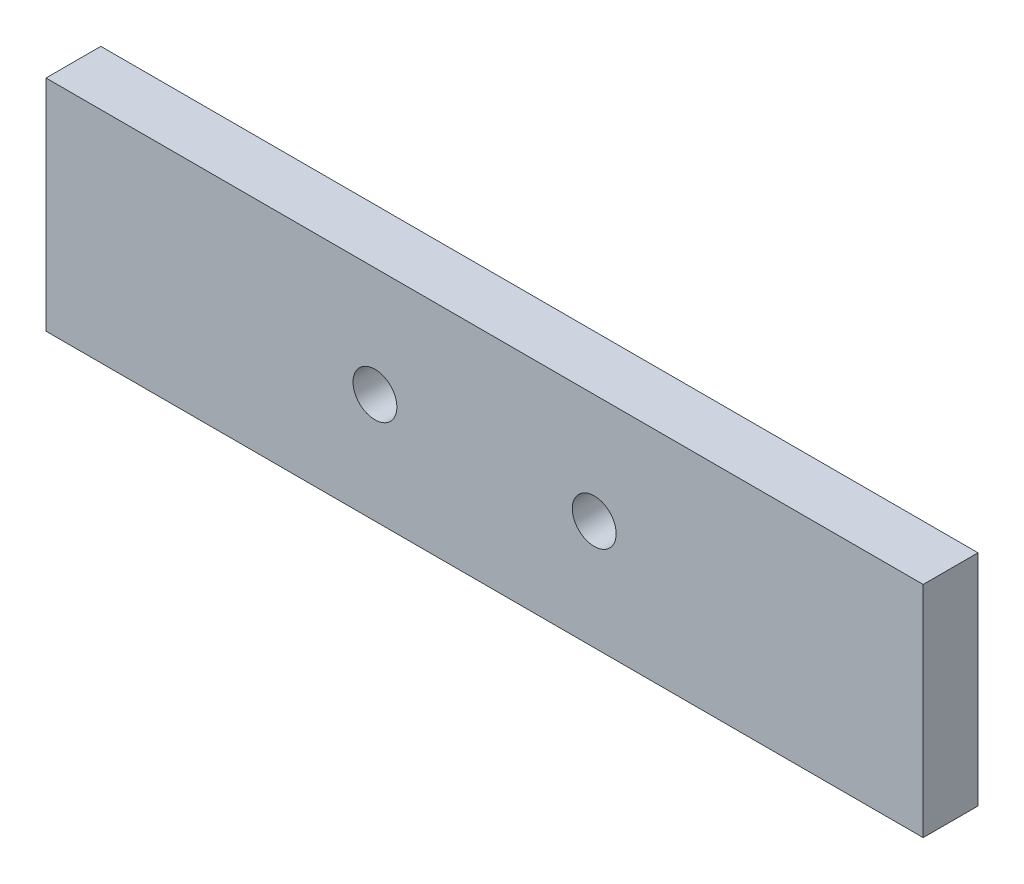
SolidWorks part; units mm, degrees
material "6063-T4"
ref_plane "Alzado" through (0, 0, 0) normal (0, 0, 1) x (1, 0, 0)
ref_plane "Planta" through (0, 0, 0) normal (0, 1, 0) x (1, 0, 0)
ref_plane "Vista lateral" through (0, 0, 0) normal (1, 0, 0) x (0, 0, -1)
sketch "Croquis1" plane through (0, 0, 0) normal (0, 0, 1) x (1, 0, 0)
  line L1 (0, 0) -> (80, 0)
  line L2 (0, 0) -> (0, 20)
  line L3 (0, 20) -> (80, 20)
  line L4 (80, 0) -> (80, 20)
  line L5 (0, 0) -> (80, 20) construction
  line L6 (0, 20) -> (80, 0) construction
  circle A0 centre (30, 10) radius 2
  circle A1 centre (50, 10) radius 2
  circle A2 centre (8, 10) radius 4.05
  circle A3 centre (72, 10) radius 4.05
  point P4 (40, 10)
  dimension "D7" = 8.1
  dimension "D8" = 4
  dimension "D1" = 80
  dimension "D2" = 20
  dimension "D3" = 20
  dimension "D4" = 10
  dimension "D5" = 32
  dimension "D6" = 64
extrude "Saliente-Extruir2" add sketch "Croquis1" along normal blind 5
ref_plane "Plano1" through (0, 0, 5) normal (0, 0, 1) x (1, 0, 0)
sketch "Croquis2" plane through (0, 0, 5) normal (0, 0, 1) x (1, 0, 0)
  circle A0 centre (8, 10) radius 6
  circle A1 centre (73, 10) radius 6
  circle A2 centre (8, 10) radius 4.05 construction
  dimension "D1" = 12
  dimension "D2" = 65
extrude "Saliente-Extruir3" add sketch "Croquis2" against normal blind 2.1 contours A1 | A0
